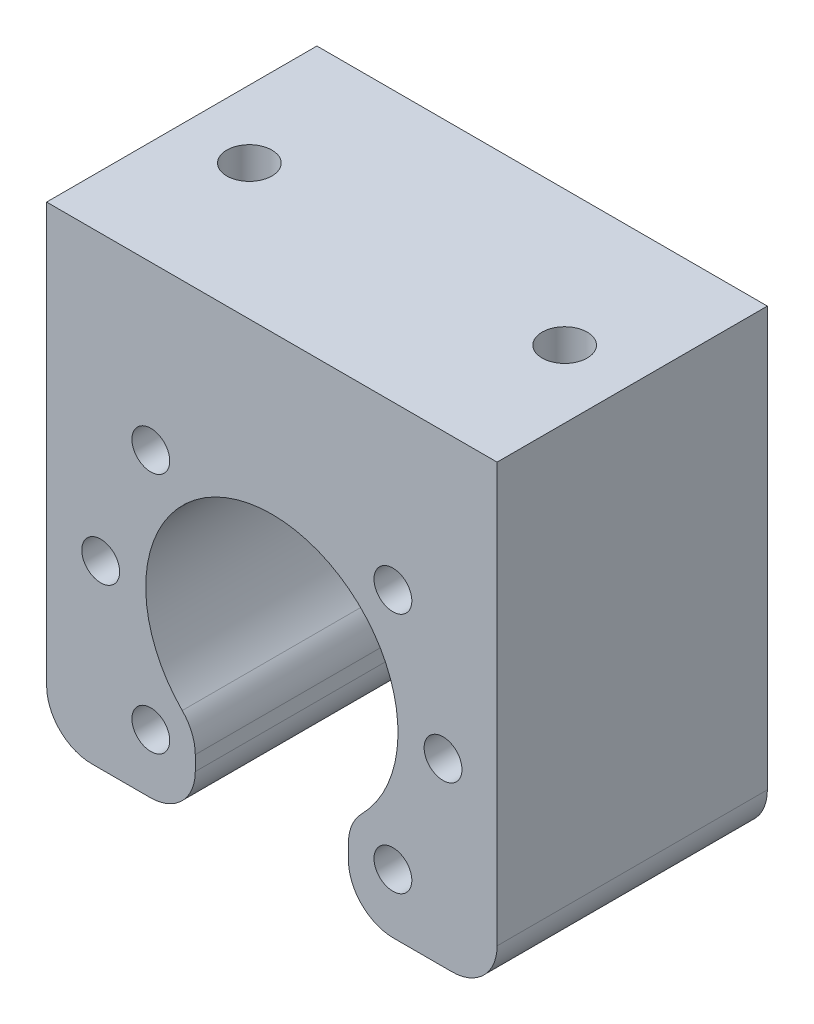
SolidWorks part; units mm, degrees
material "1023 Листовая углеродистая сталь (SS)"
ref_plane "Front" through (0, 0, 0) normal (0, 0, 1) x (1, 0, 0)
ref_plane "Top" through (0, 0, 0) normal (0, 1, 0) x (1, 0, 0)
ref_plane "Right" through (0, 0, 0) normal (1, 0, 0) x (0, 0, -1)
sketch "Sketch1" plane through (0, 0, 0) normal (0, 0, 1) x (1, 0, 0)
  line L0 (0, 0) -> (0, 31.5) construction
  line L1 (-25, 31.5) -> (25, 31.5)
  line L2 (-25, 31.5) -> (-25, -20)
  line L3 (-25, -20) -> (-8.5, -20)
  line L4 (25, 31.5) -> (25, -20)
  line L5 (8.5, -20) -> (25, -20)
  line L7 (-8.5, -11.1243) -> (-8.5, -20)
  line L9 (8.5, -11.1243) -> (8.5, -20)
  arc A0 (8.5, -11.1243) -> (-8.5, -11.1243) centre (0, 0) ccw
  dimension "D1" = 28
  dimension "D4" = 6
  dimension "D2" = 50
  dimension "D3" = 31.5
  dimension "D7" = 8.5
extrude "Extrude1" add sketch "Sketch1" along normal blind 30
fillet "Fillet1" radius 5 6 edges at (-8.5, -20, 15) (8.5, -20, 15) (8.5, -11.1243, 15) (-8.5, -11.1243, 15) (-25, -20, 15) (25, -20, 15)
hole_wizard "M5 Tapped Hole1" positions "Sketch2" profile "Sketch3" tap size "M5" standard "DIN" end condition through all
sketch "Sketch2" plane through (0, 0, 0) normal (0, 0, -1) x (-1, 0, 0)
  point P0 (-13.435, 13.435)
  point P3 (13.435, 13.435)
  point P6 (19, 0)
  point P9 (13.435, -13.435)
  point P12 (-13.435, -13.435)
  point P15 (-19, 0)
sketch "Sketch3" plane through (13.435, 13.435, 0) normal (1, 0, 0) x (0, 1, 0)
  line L0 (0, 0) -> (0, 30)
  line L1 (0, 30) -> (2.1, 30)
  line L2 (2.1, 30) -> (2.1, 0)
  line L5 (2.1, 0) -> (0, 0)
  line L11 (0, -6.35) -> (0, 107.95) construction
  dimension "Диаметр проходного сверла" = 4.2
  dimension "Глубина проходного сверла" = 30
cosmetic thread "Cosmetic Thread1" parameters "D2"=5
cosmetic thread "Cosmetic Thread2" parameters "D2"=5
cosmetic thread "Cosmetic Thread3" parameters "D2"=5
cosmetic thread "Cosmetic Thread4" parameters "D2"=5
cosmetic thread "Cosmetic Thread5" parameters "D2"=5
cosmetic thread "Cosmetic Thread6" parameters "D2"=5
hole_wizard "M6 Tapped Hole1" positions "Sketch4" profile "Sketch6" tap size "M6" standard "DIN"
sketch "Sketch4" plane through (0, 31.5, 0) normal (0, 1, 0) x (1, 0, 0)
  point P0 (-17.5, -15)
  point P3 (17.5, -15)
sketch "Sketch6" plane through (-17.5, 31.5, 15) normal (1, 0, 0) x (0, 0, 1)
  line L0 (0, 0) -> (0, 21.5022)
  line L1 (0, 21.5022) -> (2.5, 20)
  line L2 (2.5, 20) -> (2.5, 0)
  line L5 (2.5, 0) -> (0, 0)
  line L10 (0, 21.5022) -> (-2.5, 20) construction
  line L11 (0, -6.35) -> (0, 107.95) construction
  dimension "Диаметр сверла" = 5
  dimension "Глубина сверла" = 20
  dimension "Угол заточки сверла" = 118
cosmetic thread "Cosmetic Thread7" parameters "D1"=12, "D2"=6
cosmetic thread "Cosmetic Thread8" parameters "D1"=12, "D2"=6
